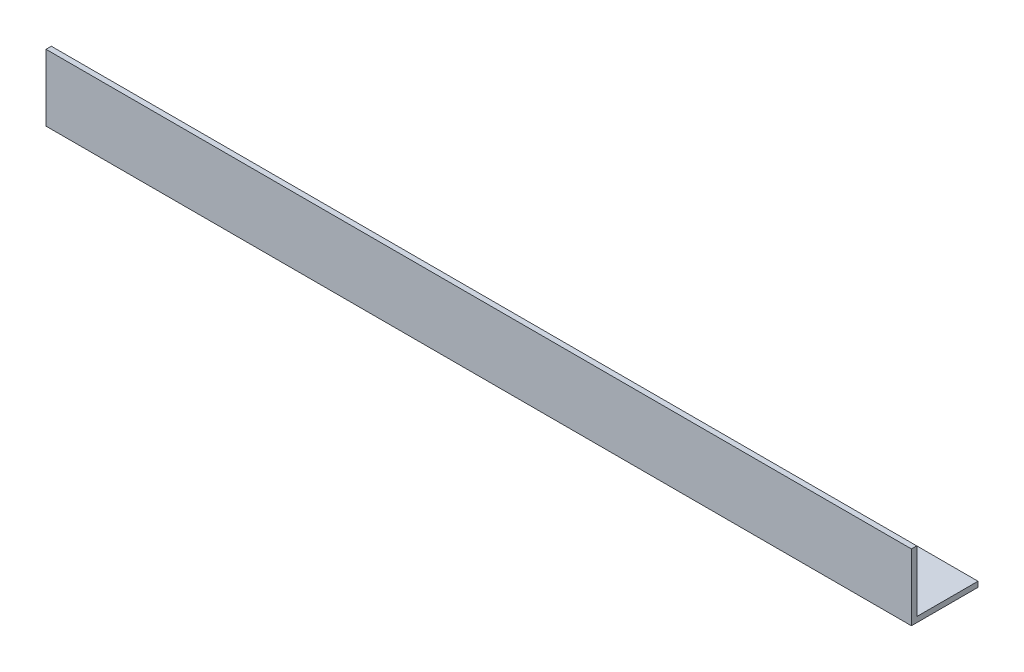
SolidWorks part; units mm, degrees
ref_plane "Спереди" through (0, 0, 0) normal (0, 0, 1) x (1, 0, 0)
ref_plane "Сверху" through (0, 0, 0) normal (0, 1, 0) x (1, 0, 0)
ref_plane "Справа" through (0, 0, 0) normal (1, 0, 0) x (0, 0, -1)
sketch "Эскиз1" plane through (0, 0, 0) normal (1, 0, 0) x (0, 0, -1)
  line L0 (0, 50) -> (0, 0)
  line L1 (0, 0) -> (50, 0)
extrude "Вытянуть-Тонкостенный1" add sketch "Эскиз1" along normal blind 650 thin thin type one direction reverse wall 4
